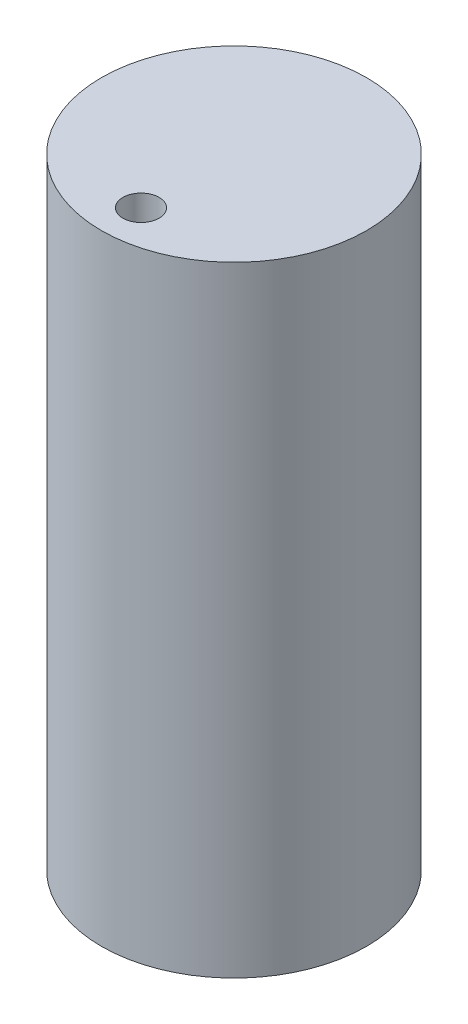
SolidWorks part; units mm, degrees
ref_plane "Front Plane" through (0, 0, 0) normal (0, 0, 1) x (1, 0, 0)
ref_plane "Top Plane" through (0, 0, 0) normal (0, 1, 0) x (1, 0, 0)
ref_plane "Right Plane" through (0, 0, 0) normal (1, 0, 0) x (0, 0, -1)
sketch "Sketch1" plane through (0, 0, 0) normal (0, 1, 0) x (1, 0, 0)
  circle A0 centre (0, 0) radius 10.69
  circle A2 centre (0, -7.5) radius 1.4577
extrude "Boss-Extrude1" add sketch "Sketch1" along normal blind 50
